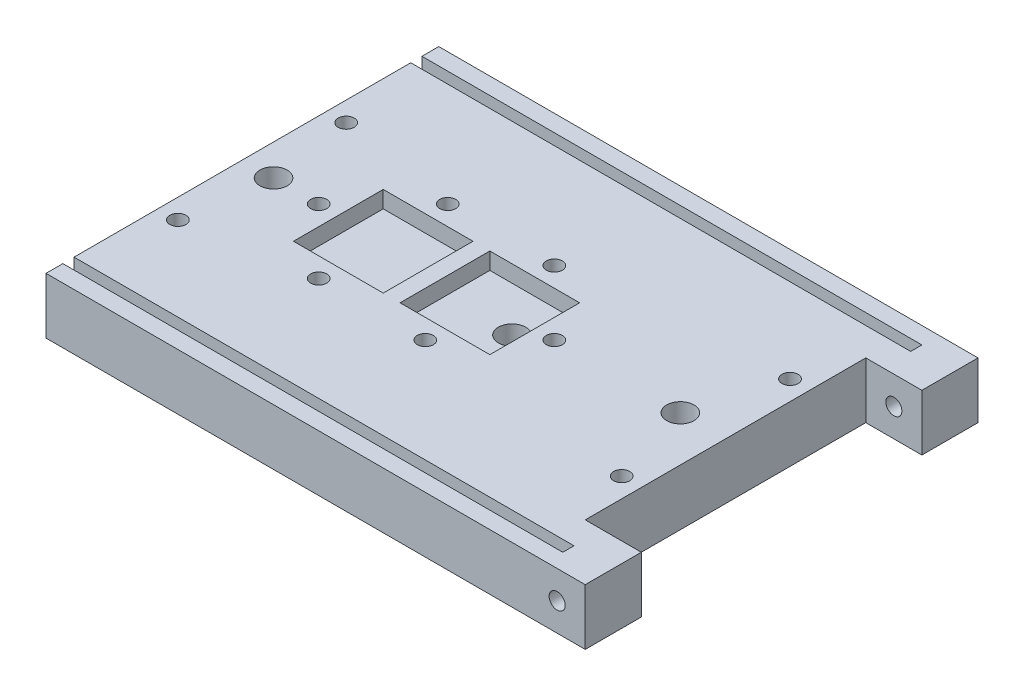
SolidWorks part; units mm, degrees
ref_plane "Alzado" through (0, 0, 0) normal (0, 0, 1) x (1, 0, 0)
ref_plane "Planta" through (0, 0, 0) normal (0, 1, 0) x (1, 0, 0)
ref_plane "Vista lateral" through (0, 0, 0) normal (1, 0, 0) x (0, 0, -1)
sketch "Croquis1" plane through (0, 0, 0) normal (0, 1, 0) x (1, 0, 0)
  line L0 (22.5, -35) -> (51.5, -35)
  line L1 (-22.5, 35) -> (22.5, 35)
  line L3 (-22.5, -35) -> (22.5, -35)
  line L4 (-22.5, -35) -> (-34.6, -35)
  line L7 (51.5, -35) -> (51.5, 35)
  line L8 (51.5, 35) -> (22.5, 35)
  line L9 (-34.6, -35) -> (-34.6, 35)
  line L10 (-34.6, 35) -> (-22.5, 35)
  point P0 (0, 0)
  dimension "D1" = 70
  dimension "D2" = 45
  dimension "D3" = 29
  dimension "D4" = 12.1
  dimension "D5" = 51.5
  dimension "D6" = 35
  dimension "D7" = 35
extrude "Saliente-Extruir1" add sketch "Croquis1" along normal blind 10
sketch "Croquis2" plane through (0, 10, 0) normal (0, 1, 0) x (1, 0, 0)
  line L0 (51.5, -35) -> (51.5, 35) construction
  line L2 (1.5, 8) -> (17.5, 8)
  line L4 (1.5, 8) -> (1.5, -8)
  line L5 (1.5, -8) -> (17.5, -8)
  line L6 (17.5, 8) -> (17.5, -8)
  line L7 (1.5, 8) -> (17.5, -8) construction
  line L8 (1.5, -8) -> (17.5, 8) construction
  line L9 (51.5, 35) -> (-34.6, 35) construction
  point P0 (9.5, 0)
  dimension "D1" = 42
  dimension "D2" = 35
  dimension "D4" = 16
  dimension "D6" = 16
sketch "Croquis7" plane through (0, 10, 0) normal (0, 1, 0) x (1, 0, 0)
  line L1 (-34.6, 32) -> (51.5, 32)
  line L2 (-34.6, 32) -> (-34.6, 30)
  line L3 (-34.6, 30) -> (51.5, 30)
  line L4 (51.5, 32) -> (51.5, 30)
  line L7 (51.5, 35) -> (-34.6, 35) construction
  line L9 (51.5, -35) -> (51.5, 35) construction
  line L10 (-34.6, 35) -> (-34.6, -35) construction
  dimension "D1" = 2
  dimension "D2" = 3
extrude "Cortar-Extruir4" cut sketch "Croquis7" against normal blind 3
mirror "Simetría2" about plane through (0, 0, 0) normal (0, 0, 1) of "Cortar-Extruir4"
sketch "Croquis15" plane through (0, 10, 0) normal (0, 1, 0) x (1, 0, 0)
  line L0 (-34.6, -35) -> (51.5, -35) construction
  line L2 (-34.6, 30) -> (-34.6, -30) construction
  circle A0 centre (-31.1, -15) radius 1.435
  dimension "D1" = 2.87
  dimension "D2" = 20
  dimension "D3" = 3.5
extrude "Cortar-Extruir10" cut sketch "Croquis15" against normal up to next (10 mm away)
mirror "Simetría4" about plane through (0, 0, 0) normal (0, 0, 1) of "Cortar-Extruir10"
sketch "Croquis16" plane through (51.5, 0, 0) normal (1, 0, 0) x (0, 0, -1)
  line L0 (-35, 0) -> (35, 0) construction
  line L1 (-35, 10) -> (-25, 10)
  line L2 (-35, 10) -> (-35, 0)
  line L3 (-35, 0) -> (-25, 0)
  line L4 (-25, 10) -> (-25, 0)
  dimension "D1" = 10
extrude "Saliente-Extruir7" add sketch "Croquis16" along normal blind 10
sketch "Croquis17" plane through (0, 10, 0) normal (0, 1, 0) x (1, 0, 0)
  line L1 (51.5, -30) -> (54.5, -30)
  line L2 (51.5, -30) -> (51.5, -32)
  line L3 (51.5, -32) -> (54.5, -32)
  line L4 (54.5, -30) -> (54.5, -32)
  dimension "D1" = 2
  dimension "D2" = 3
extrude "Cortar-Extruir11" cut sketch "Croquis17" against normal blind 3
mirror "Simetría5" about plane through (0, 0, 0) normal (0, 0, 1) of "Saliente-Extruir7", "Cortar-Extruir11"
sketch "Croquis18" plane through (0, 10, 0) normal (0, 1, 0) x (1, 0, 0)
  line L0 (51.5, -25) -> (51.5, 25) construction
  line L1 (61.5, 35) -> (-34.6, 35) construction
  circle A0 centre (48, 15) radius 1.435
  dimension "D1" = 2.87
  dimension "D2" = 3.5
  dimension "D3" = 20
extrude "Cortar-Extruir12" cut sketch "Croquis18" against normal up to next (10 mm away)
mirror "Simetría6" about plane through (0, 0, 0) normal (0, 0, 1) of "Cortar-Extruir12"
sketch "Croquis19" plane through (-34.6, 0, 0) normal (-1, 0, 0) x (0, 0, 1)
  line L0 (35, 10) -> (35, 0) construction
  line L1 (-35, 0) -> (35, 0) construction
  circle A0 centre (26.5, 5) radius 1.435
  point P4 (35, 5)
  dimension "D1" = 2.87
  dimension "D2" = 8.5
  dimension "D3" = 5
extrude "Cortar-Extruir13" cut sketch "Croquis19" against normal blind 10
mirror "Simetría7" about plane through (0, 0, 0) normal (0, 0, 1) of "Cortar-Extruir13"
sketch "Croquis20" plane through (0, 0, 35) normal (0, 0, 1) x (1, 0, 0)
  line L0 (61.5, 10) -> (61.5, 0) construction
  line L1 (-34.6, 0) -> (61.5, 0) construction
  circle A0 centre (56.5, 5) radius 1.435
  dimension "D1" = 2.87
  dimension "D2" = 5
  dimension "D3" = 5
extrude "Cortar-Extruir14" cut sketch "Croquis20" against normal up to next (10 mm away)
mirror "Simetría8" about plane through (0, 0, 0) normal (0, 0, 1) of "Cortar-Extruir14"
sketch "Croquis21" plane through (0, 0, 0) normal (0, -1, 0) x (1, 0, 0)
  line L0 (61.5, 35) -> (61.5, 25) construction
  line L2 (-34.6, 35) -> (61.5, 35) construction
  circle A0 centre (13.45, 0) radius 2.435
  circle A1 centre (43.45, 0) radius 2.435
  circle A2 centre (-29.05, 0) radius 2.435
  dimension "D2" = 4.87
  dimension "D4" = 4.87
  dimension "D5" = 4.87
  dimension "D1" = 48.05
  dimension "D3" = 35
  dimension "D6" = 35
  dimension "D7" = 35
  dimension "D8" = 42.5
  dimension "D9" = 30
extrude "Cortar-Extruir15" cut sketch "Croquis21" against normal blind 10
extrude "Cortar-Extruir16" cut sketch "Croquis2" against normal blind 3 contours L5 L6 L2 L4
mirror "Simetría9" about plane through (0, 0, 0) normal (1, 0, 0) of "Cortar-Extruir16"
sketch "Croquis22" plane through (0, 10, 0) normal (0, 1, 0) x (1, 0, 0)
  line L0 (-1.5, 8) -> (-1.5, -8) construction
  line L1 (-1.5, 8) -> (-17.5, 8) construction
  line L2 (-17.5, 8) -> (-17.5, -8) construction
  line L3 (-1.5, 8) -> (-17.5, 8) construction
  line L5 (-1.5, -8) -> (-17.5, -8) construction
  circle A0 centre (-9.5, 11.5) radius 1.435
  circle A1 centre (-21, 0) radius 1.435
  circle A2 centre (-9.5, -11.5) radius 1.435
  point P10 (0, 0)
  point P15 (0, 0)
  dimension "D1" = 2.87
  dimension "D4" = 2.87
  dimension "D5" = 2.87
  dimension "D2" = 8
  dimension "D3" = 3.5
  dimension "D6" = 3.5
  dimension "D7" = 8
  dimension "D8" = 3.5
  dimension "D9" = 8
extrude "Cortar-Extruir17" cut sketch "Croquis22" against normal up to next (10 mm away)
mirror "Simetría10" about plane through (0, 0, 0) normal (1, 0, 0) of "Cortar-Extruir17"
